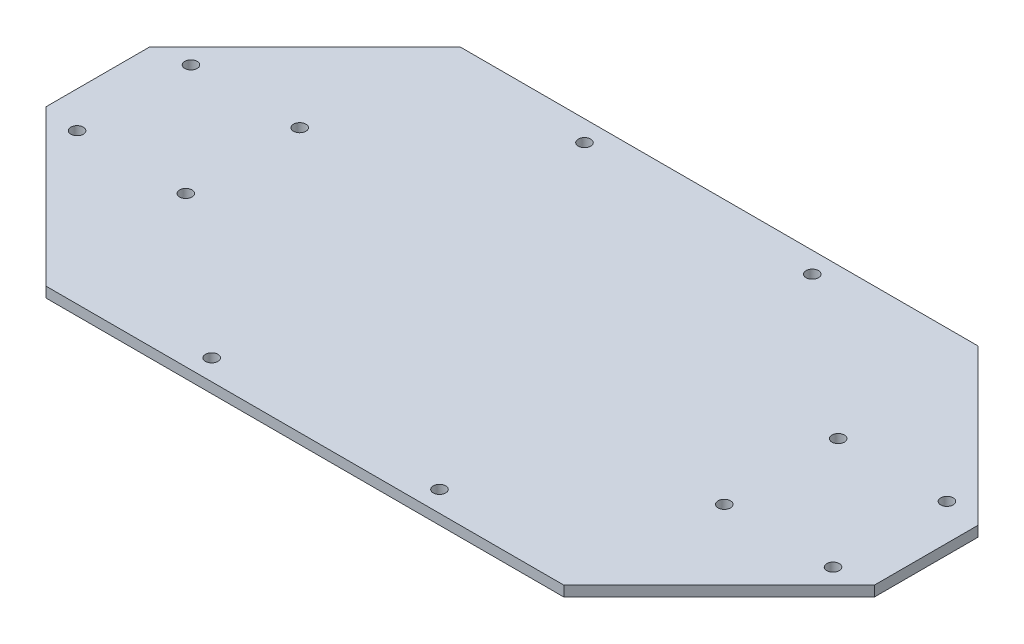
SolidWorks part; units mm, degrees
material "Pin"
ref_plane "Plan de face" through (0, 0, 0) normal (0, 0, 1) x (1, 0, 0)
ref_plane "Plan de dessus" through (0, 0, 0) normal (0, 1, 0) x (1, 0, 0)
ref_plane "Plan de droite" through (0, 0, 0) normal (1, 0, 0) x (0, 0, -1)
sketch "Esquisse1" plane through (0, 0, 0) normal (0, 1, 0) x (1, 0, 0)
  line L1 (0, 0) -> (160, 0)
  line L2 (0, 0) -> (0, 80)
  line L3 (0, 80) -> (160, 80)
  line L4 (160, 0) -> (160, 80)
  dimension "D1" = 160
  dimension "D2" = 80
extrude "Boss.-Extru.1" add sketch "Esquisse1" along normal blind 2
sketch "Esquisse2" plane through (0, 2, 0) normal (0, 1, 0) x (1, 0, 0)
  line L0 (0, 30) -> (30, 0)
  line L1 (0, 80) -> (0, 0) construction
  line L2 (0, 0) -> (160, 0) construction
  line L3 (30, 0) -> (0, 0)
  line L4 (0, 0) -> (0, 30)
  line L5 (30, 80) -> (0, 50)
  line L6 (160, 80) -> (0, 80) construction
  line L7 (0, 50) -> (0, 80)
  line L8 (0, 80) -> (30, 80)
  line L9 (130, 80) -> (160, 80)
  line L10 (160, 80) -> (160, 50)
  line L11 (160, 0) -> (160, 80) construction
  line L12 (160, 50) -> (130, 80)
  line L13 (160, 30) -> (130, 0)
  line L14 (130, 0) -> (160, 0)
  line L15 (160, 0) -> (160, 30)
  dimension "D1" = 30
  dimension "D2" = 30
  dimension "D3" = 30
  dimension "D4" = 30
  dimension "D5" = 30
  dimension "D6" = 30
  dimension "D7" = 30
  dimension "D8" = 30
extrude "Enlèv. mat.-Extru.1" cut sketch "Esquisse2" against normal blind 2
hole_wizard "Dégagement M21" positions "Esquisse3" profile "Esquisse4" size "M2" standard "ISO" slot yes end condition through all
sketch "Esquisse3" plane through (0, 2, 0) normal (0, 1, 0) x (1, 0, 0)
  point P0 (7, 51)
  point P3 (7, 29)
  point P6 (28, 29)
  point P9 (28, 51)
  point P12 (58, 76)
  point P15 (58, 4)
  point P18 (132, 29)
  point P21 (153, 29)
  point P24 (153, 51)
  point P27 (132, 51)
  point P30 (101.995, 76)
  point P32 (101.995, 4)
sketch "Esquisse4" plane through (7, 2, -51) normal (1, 0, 0) x (0, 0, 1)
  line L0 (0, 0) -> (0, 2)
  line L1 (0, 2) -> (1.2, 2)
  line L2 (1.2, 2) -> (1.2, 0)
  line L5 (1.2, 0) -> (0, 0)
  line L11 (0, -6.35) -> (0, 107.95) construction
  dimension "Diamètre du perçage jusqu'au prochain" = 2.4
  dimension "Profondeur du perçage jusqu'au prochain" = 2
